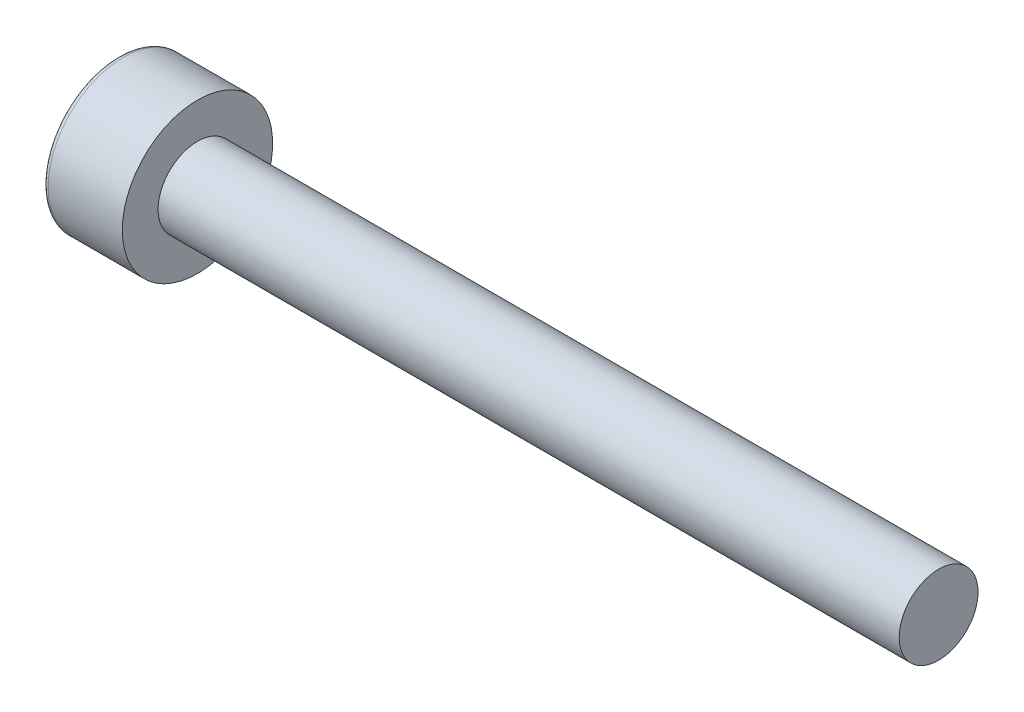
SolidWorks part; units mm, degrees
material "AISI 304"
ref_plane "前视基准面" through (0, 0, 0) normal (0, 0, 1) x (1, 0, 0)
ref_plane "上视基准面" through (0, 0, 0) normal (0, 1, 0) x (1, 0, 0)
ref_plane "右视基准面" through (0, 0, 0) normal (1, 0, 0) x (0, 0, -1)
sketch "草图1" plane through (0, 0, 0) normal (0, 0, 1) x (1, 0, 0)
  line L0 (0, 0) -> (9.1986, 0) construction
  line L1 (0, 0) -> (0, 2.84)
  line L2 (0, 2.84) -> (3, 2.84)
  line L3 (3, 2.84) -> (3, 1.49)
  line L4 (3, 1.49) -> (31, 1.49)
  line L5 (31, 1.49) -> (31, 0)
  line L6 (31, 0) -> (0, 0)
  dimension "D1" = 2.98
  dimension "长度" = 28
  dimension "D2" = 3
  dimension "D3" = 5.68
revolve "旋转1" add sketch "草图1" angle 360 about L0
cosmetic thread "装饰螺纹线1" parameters "D2"=2.459
sketch "草图2" plane through (0, 0, 0) normal (-1, 0, 0) x (0, 0, 1)
  line L1 (-1.4434, 0) -> (-0.7217, -1.25)
  line L2 (-0.7217, -1.25) -> (0.7217, -1.25)
  line L3 (0.7217, -1.25) -> (1.4434, 0)
  line L4 (1.4434, 0) -> (0.7217, 1.25)
  line L5 (0.7217, 1.25) -> (-0.7217, 1.25)
  line L6 (-0.7217, 1.25) -> (-1.4434, 0)
  circle A0 centre (0, 0) radius 1.25 construction
  dimension "D1" = 2.5
extrude "切除-拉伸1" cut sketch "草图2" against normal blind 1.3
fillet "圆角1" radius 0.2 1 edges at (0, 0, 2.84)
